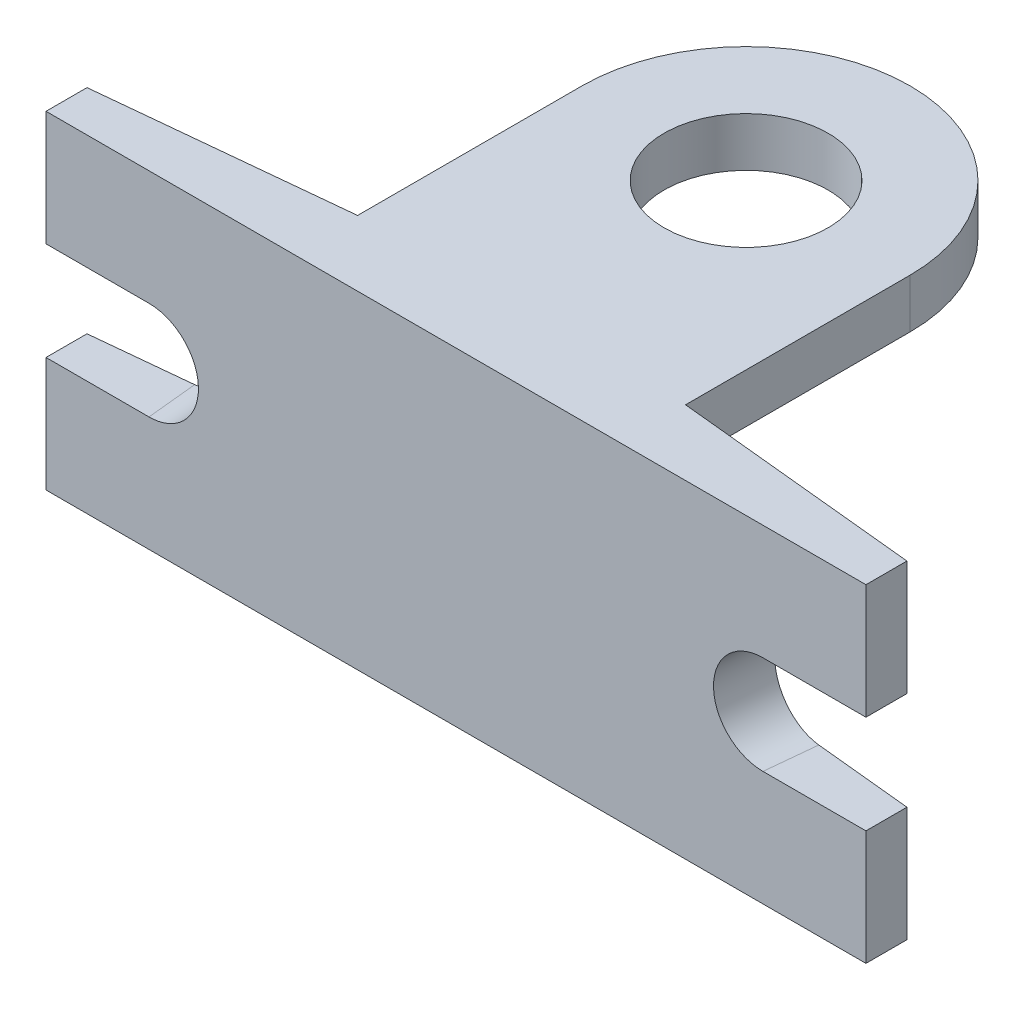
SolidWorks part; units mm, degrees
ref_plane "Front Plane" through (0, 0, 0) normal (0, 0, 1) x (1, 0, 0)
ref_plane "Top Plane" through (0, 0, 0) normal (0, 1, 0) x (1, 0, 0)
ref_plane "Right Plane" through (0, 0, 0) normal (1, 0, 0) x (0, 0, -1)
sketch "Sketch1" plane through (0, 0, 0) normal (0, 1, 0) x (1, 0, 0)
  line L0 (0, 184.3905) -> (0, 50) construction
  line L1 (-362.5622, 0) -> (345.7711, 0) construction
  line L2 (-250, 0) -> (250, 0)
  line L3 (250, 0) -> (250, 25)
  line L4 (250, 25) -> (100, 40)
  line L5 (100, 40) -> (100, 50)
  line L6 (100, 50) -> (-100, 50)
  line L8 (-100, 40) -> (-100, 50)
  line L9 (-250, 0) -> (-250, 25)
  line L10 (-250, 25) -> (-100, 40)
  line L11 (0, 0) -> (0, -206.7786) construction
  dimension "D2" = 25
  dimension "D3" = 40
  dimension "D4" = 50
  dimension "D6" = 150
extrude "Boss-Extrude1" add sketch "Sketch1" along normal blind 200
sketch "Sketch2" plane through (0, 0, -50) normal (0, 0, -1) x (-1, 0, 0)
  line L0 (0, 270.4144) -> (0, 90.4) construction
  line L1 (-292.4422, 90.4) -> (284.6437, 90.4) construction
  line L2 (-100, 0) -> (100, 0) construction
  line L3 (-40, 0) -> (40, 0)
  line L4 (-40, 90.4) -> (-40, 0)
  line L5 (40, 90.4) -> (40, 0)
  line L6 (0, 50.4) -> (0, -89.6145) construction
  arc A0 (40, 90.4) -> (-40, 90.4) centre (0, 90.4) ccw
  dimension "D1" = 80
extrude "Cut-Extrude1" cut sketch "Sketch2" against normal blind 30
sketch "Sketch3" plane through (-4.9505, 0, -49.505) normal (-0.0995, 0, -0.995) x (-0.995, 0, 0.0995)
  line L0 (363.3376, 100) -> (80.9451, 100) construction
  line L1 (186.2717, 247.1696) -> (186.2717, -26.6053) construction
  line L2 (0, 266.3935) -> (0, -116.7588) construction
  line L3 (186.2717, 130) -> (296.3854, 130)
  line L4 (296.3854, 130) -> (296.3854, 70)
  line L5 (296.3854, 70) -> (186.2717, 70)
  line L6 (246.2717, 200) -> (246.2717, 0) construction
  arc A0 (186.2717, 130) -> (186.2717, 70) centre (186.2717, 100) ccw
  dimension "D1" = 60
  dimension "D2" = 60
extrude "Cut-Extrude2" cut sketch "Sketch3" against normal through all
sketch "Sketch4" plane through (4.9505, 0, -49.505) normal (0.0995, 0, -0.995) x (-0.995, 0, -0.0995)
  line L0 (-186.2717, 264.7147) -> (-186.2717, -37.0496) construction
  line L1 (-381.3789, 100) -> (-77.625, 100) construction
  line L3 (-246.2717, 200) -> (-246.2717, 0) construction
  line L4 (-186.2717, 130) -> (-315.6003, 130)
  line L5 (-315.6003, 130) -> (-315.6003, 70)
  line L6 (-315.6003, 70) -> (-186.2717, 70)
  arc A0 (-186.2717, 70) -> (-186.2717, 130) centre (-186.2717, 100) ccw
  dimension "D1" = 60
  dimension "D2" = 60
extrude "Cut-Extrude3" cut sketch "Sketch4" against normal through all
ref_plane "Plane1" through (0, 200, 0) normal (0, 1, 0) x (1, 0, 0)
sketch "Sketch5" plane through (0, 200, 0) normal (0, 1, 0) x (1, 0, 0)
  line L0 (0, 334.3336) -> (0, -135.4858) construction
  line L1 (-308.8189, 0) -> (401.7506, 0) construction
  line L2 (100, 50) -> (-100, 50) construction
  line L3 (100, 50) -> (-100, 50)
  line L4 (100, 50) -> (100, 176.9075)
  line L5 (-100, 50) -> (-100, 176.9075)
  arc A0 (100, 176.9075) -> (-100, 176.9075) centre (0, 176.9075) ccw
  circle A1 centre (0, 176.9075) radius 50
  dimension "D2" = 100
extrude "Boss-Extrude2" add sketch "Sketch5" against normal blind 30
